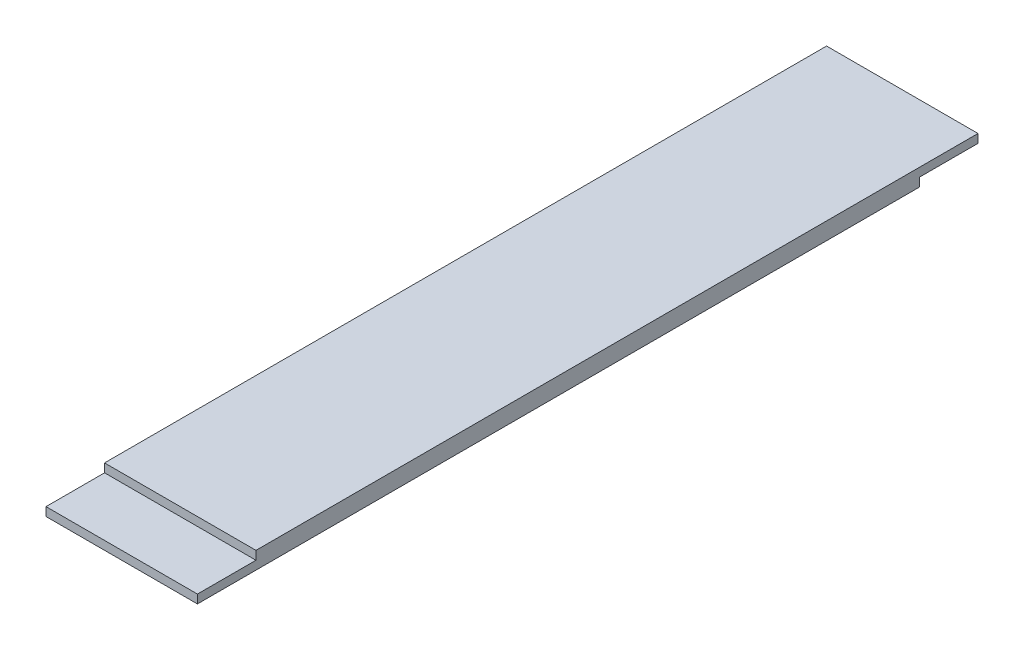
SolidWorks part; units mm, degrees
ref_plane "前基準面" through (0, 0, 0) normal (0, 0, 1) x (1, 0, 0)
ref_plane "上基準面" through (0, 0, 0) normal (0, 1, 0) x (1, 0, 0)
ref_plane "右基準面" through (0, 0, 0) normal (1, 0, 0) x (0, 0, -1)
sketch "草圖1" plane through (0, 0, 0) normal (0, 1, 0) x (1, 0, 0)
  line L1 (-19.4, -100) -> (19.4, -100)
  line L2 (-19.4, -100) -> (-19.4, 100)
  line L3 (-19.4, 100) -> (19.4, 100)
  line L4 (19.4, -100) -> (19.4, 100)
  line L5 (-19.4, -100) -> (19.4, 100) construction
  line L6 (-19.4, 100) -> (19.4, -100) construction
  point P0 (0, 0)
  dimension "D1" = 200
  dimension "D2" = 38.8
extrude "填料-伸長1" add sketch "草圖1" along normal blind 4.4
sketch "草圖3" plane through (0, 4.4, 0) normal (0, 1, 0) x (1, 0, 0)
  line L0 (19.4, -100) -> (19.4, 100) construction
  line L1 (-19.4, -100) -> (19.4, -100)
  line L2 (-19.4, -100) -> (-19.4, -85)
  line L3 (-19.4, -85) -> (19.4, -85)
  line L4 (19.4, -100) -> (19.4, -85)
  dimension "D1" = 15
extrude "除料-伸長1" cut sketch "草圖3" against normal blind 2.2
sketch "草圖4" plane through (0, 0, 0) normal (0, -1, 0) x (1, 0, 0)
  line L0 (19.4, 100) -> (19.4, -100) construction
  line L1 (-19.4, -100) -> (19.4, -100)
  line L2 (-19.4, -100) -> (-19.4, -85)
  line L3 (-19.4, -85) -> (19.4, -85)
  line L4 (19.4, -100) -> (19.4, -85)
  dimension "D1" = 15
extrude "除料-伸長2" cut sketch "草圖4" against normal blind 2.2
